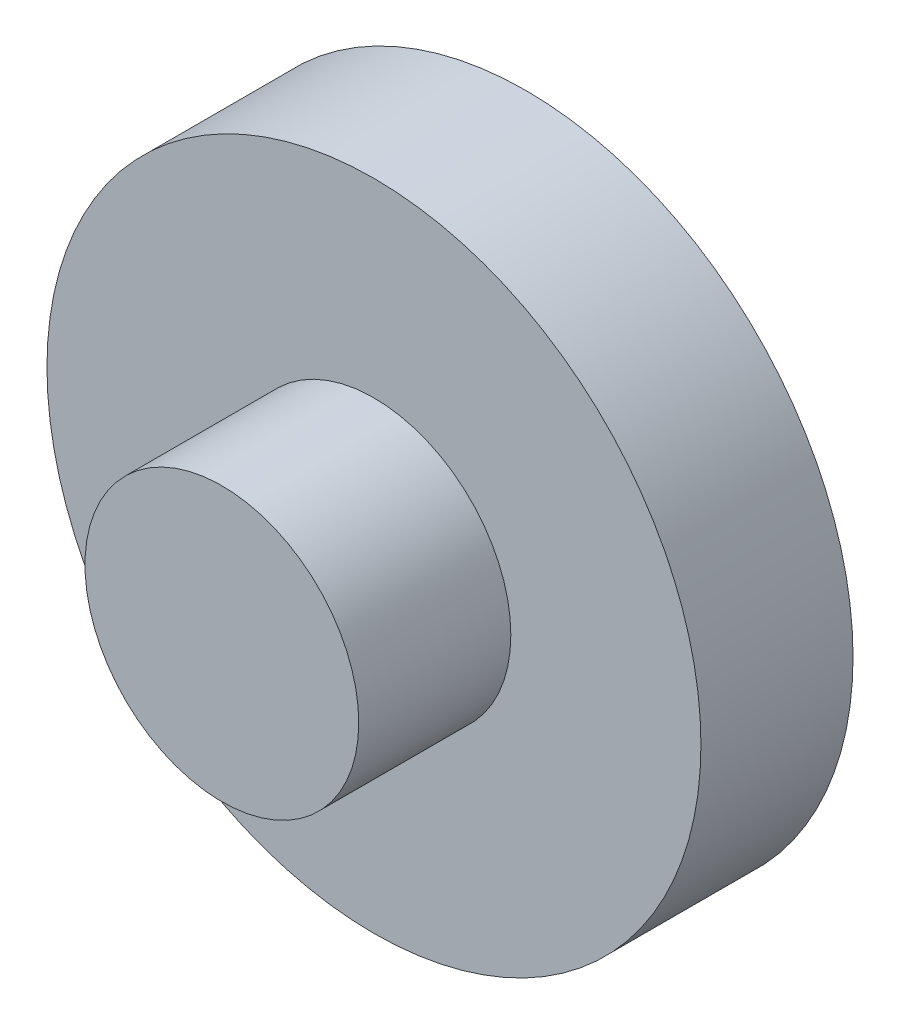
SolidWorks part; units mm, degrees
ref_plane "Front Plane" through (0, 0, 0) normal (0, 0, 1) x (1, 0, 0)
ref_plane "Top Plane" through (0, 0, 0) normal (0, 1, 0) x (1, 0, 0)
ref_plane "Right Plane" through (0, 0, 0) normal (1, 0, 0) x (0, 0, -1)
sketch "Sketch1" plane through (0, 0, 0) normal (0, 0, 1) x (1, 0, 0)
  circle A0 centre (0, 0) radius 5.461
  dimension "D1" = 10.922
extrude "Boss-Extrude1" add sketch "Sketch1" along normal blind 2.54 contours A0
sketch "Sketch2" plane through (0, 0, 2.54) normal (0, 0, 1) x (1, 0, 0)
  circle A0 centre (0, 0) radius 2.286
  dimension "D1" = 4.572
extrude "Boss-Extrude2" add sketch "Sketch2" along normal blind 2.54
